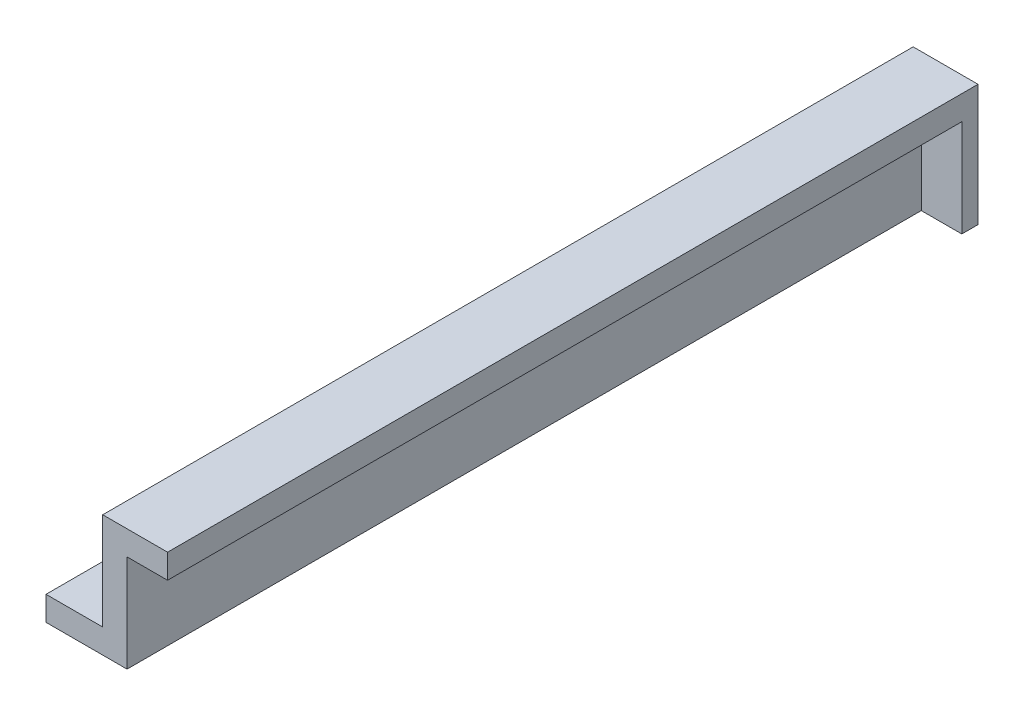
SolidWorks part; units mm, degrees
ref_plane "Front Plane" through (0, 0, 0) normal (0, 0, 1) x (1, 0, 0)
ref_plane "Top Plane" through (0, 0, 0) normal (0, 1, 0) x (1, 0, 0)
ref_plane "Right Plane" through (0, 0, 0) normal (1, 0, 0) x (0, 0, -1)
sketch "Sketch1" plane through (0, 0, 0) normal (0, 0, 1) x (1, 0, 0)
  line L0 (0, 0) -> (7, 0)
  line L1 (7, 0) -> (7, 12)
  line L2 (7, 12) -> (15, 12)
  line L3 (0, -3) -> (10, -3)
  line L4 (10, -3) -> (10, 9)
  line L5 (10, 9) -> (15, 9)
  line L6 (15, 12) -> (15, 9)
  line L7 (0, 0) -> (0, -3)
  dimension "D1" = 7
  dimension "D2" = 3
  dimension "D3" = 8
  dimension "D4" = 15
extrude "Boss-Extrude1" add sketch "Sketch1" along normal blind 100
sketch "Sketch2" plane through (0, 0, 0) normal (0, 1, 0) x (1, 0, 0)
  line L0 (3.5, 0) -> (3.5, -100) construction
  line L1 (7, 0) -> (0, 0) construction
  line L2 (7, -100) -> (0, -100) construction
  line L3 (0, -50) -> (7, -50) construction
  line L4 (0, -100) -> (0, 0) construction
  line L5 (7, -100) -> (7, 0) construction
  circle A0 centre (3.5, -10) radius 2
  circle A1 centre (3.5, -90) radius 2
  circle A2 centre (3.5, -50) radius 2
  dimension "D1" = 4
  dimension "D2" = 4
  dimension "D5" = 4
  dimension "D3" = 80
  dimension "D4" = 40
extrude "Cut-Extrude1" cut sketch "Sketch2" against normal blind 100
sketch "Sketch3" plane through (0, 0, 0) normal (0, 0, -1) x (-1, 0, 0)
  line L1 (-10, 9) -> (-15, 9)
  line L2 (-10, 9) -> (-10, -3)
  line L3 (-10, -3) -> (-15, -3)
  line L4 (-15, 9) -> (-15, -3)
extrude "Boss-Extrude2" add sketch "Sketch3" against normal blind 2
